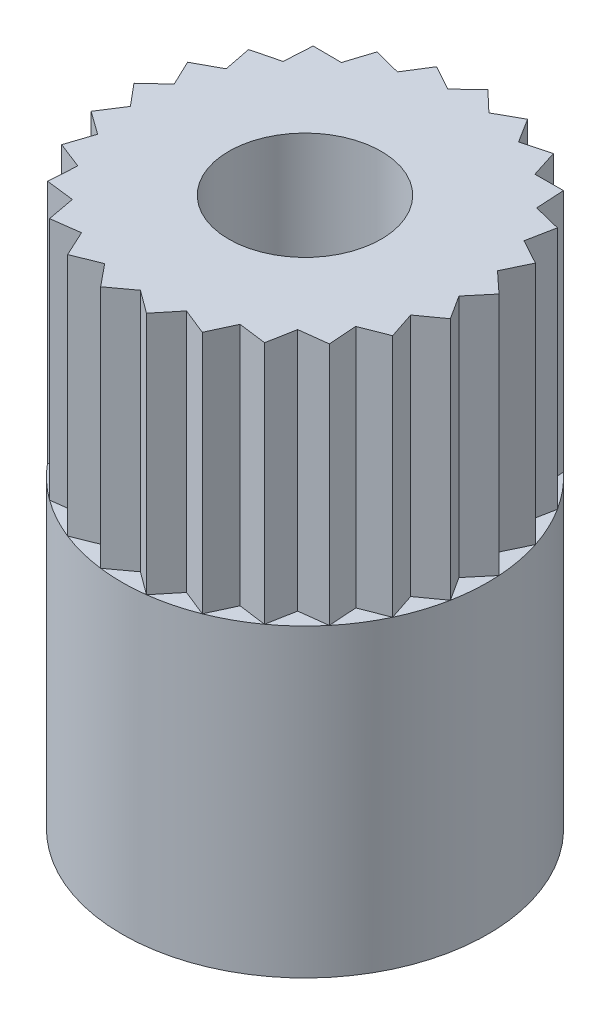
SolidWorks part; units mm, degrees
ref_plane "Front" through (0, 0, 0) normal (0, 0, 1) x (1, 0, 0)
ref_plane "Top" through (0, 0, 0) normal (0, 1, 0) x (1, 0, 0)
ref_plane "Right" through (0, 0, 0) normal (1, 0, 0) x (0, 0, -1)
sketch "Эскиз1" plane through (0, 0, 0) normal (0, 1, 0) x (1, 0, 0)
  circle A0 centre (0, 0) radius 3
  dimension "D1" = 6
extrude "Бобышка-Вытянуть1" add sketch "Эскиз1" along normal blind 5 and the other way blind 4
sketch "Эскиз2" plane through (0, 5, 0) normal (0, 1, 0) x (1, 0, 0)
  line L0 (0, 3) -> (0, -3) construction
  line L1 (0, 0) -> (0.376, 2.9763) construction
  line L2 (0, 3) -> (0.3384, 2.6787)
  line L3 (0, 3) -> (-0.3384, 2.6787)
  line L4 (0.7461, 2.9057) -> (0.3384, 2.6787)
  line L5 (0.7461, 2.9057) -> (0.9939, 2.5104)
  line L6 (1.4453, 2.6289) -> (0.9939, 2.5104)
  line L7 (1.4453, 2.6289) -> (1.587, 2.1843)
  line L8 (2.0536, 2.1869) -> (1.587, 2.1843)
  line L9 (2.0536, 2.1869) -> (2.0804, 1.721)
  line L10 (2.533, 1.6075) -> (2.0804, 1.721)
  line L11 (2.533, 1.6075) -> (2.443, 1.1496)
  line L12 (2.8532, 0.9271) -> (2.443, 1.1496)
  line L13 (2.8532, 0.9271) -> (2.6522, 0.5059)
  line L14 (2.9941, 0.1884) -> (2.6522, 0.5059)
  line L15 (2.9941, 0.1884) -> (2.6947, -0.1695)
  line L16 (2.9469, -0.5621) -> (2.6947, -0.1695)
  line L17 (2.9469, -0.5621) -> (2.5679, -0.8343)
  line L18 (2.7145, -1.2773) -> (2.5679, -0.8343)
  line L19 (2.7145, -1.2773) -> (2.2797, -1.4467)
  line L20 (2.3115, -1.9123) -> (2.2797, -1.4467)
  line L21 (2.3115, -1.9123) -> (1.8483, -1.9682)
  line L22 (1.7634, -2.4271) -> (1.8483, -1.9682)
  line L23 (1.7634, -2.4271) -> (1.3007, -2.366)
  line L24 (1.1044, -2.7893) -> (1.3007, -2.366)
  line L25 (1.1044, -2.7893) -> (0.6715, -2.6152)
  line L26 (0.376, -2.9763) -> (0.6715, -2.6152)
  line L27 (0.376, -2.9763) -> (0, -2.7)
  line L28 (-0.376, -2.9763) -> (0, -2.7)
  line L29 (-0.376, -2.9763) -> (-0.6715, -2.6152)
  line L30 (-1.1044, -2.7893) -> (-0.6715, -2.6152)
  line L31 (-1.1044, -2.7893) -> (-1.3007, -2.366)
  line L32 (-1.7634, -2.4271) -> (-1.3007, -2.366)
  line L33 (-1.7634, -2.4271) -> (-1.8483, -1.9682)
  line L34 (-2.3115, -1.9123) -> (-1.8483, -1.9682)
  line L35 (-2.3115, -1.9123) -> (-2.2797, -1.4467)
  line L36 (-2.7145, -1.2773) -> (-2.2797, -1.4467)
  line L37 (-2.7145, -1.2773) -> (-2.5679, -0.8343)
  line L38 (-2.9469, -0.5621) -> (-2.5679, -0.8343)
  line L39 (-2.9469, -0.5621) -> (-2.6947, -0.1695)
  line L40 (-2.9941, 0.1884) -> (-2.6947, -0.1695)
  line L41 (-2.9941, 0.1884) -> (-2.6522, 0.5059)
  line L42 (-2.8532, 0.9271) -> (-2.6522, 0.5059)
  line L43 (-2.8532, 0.9271) -> (-2.443, 1.1496)
  line L44 (-2.533, 1.6075) -> (-2.443, 1.1496)
  line L45 (-2.533, 1.6075) -> (-2.0804, 1.721)
  line L46 (-2.0536, 2.1869) -> (-2.0804, 1.721)
  line L47 (-2.0536, 2.1869) -> (-1.587, 2.1843)
  line L48 (-1.4453, 2.6289) -> (-1.587, 2.1843)
  line L49 (-1.4453, 2.6289) -> (-0.9939, 2.5104)
  line L50 (-0.7461, 2.9057) -> (-0.9939, 2.5104)
  line L51 (-0.7461, 2.9057) -> (-0.3384, 2.6787)
  circle A0 centre (0, 0) radius 2.7 construction
  circle A1 centre (0, 0) radius 3 construction
  point P86 (0, 0)
  dimension "D1" = 5.4
  dimension "D2" = 7.2
  dimension "D3" = 25
extrude "Вырез-Вытянуть1" cut sketch "Эскиз2" against normal blind 4 flip side to cut
sketch "Эскиз3" plane through (0, 5, 0) normal (0, 1, 0) x (1, 0, 0)
  circle A0 centre (0, 0) radius 1.25
  dimension "D1" = 2.5
extrude "Вырез-Вытянуть2" cut sketch "Эскиз3" against normal blind 7
